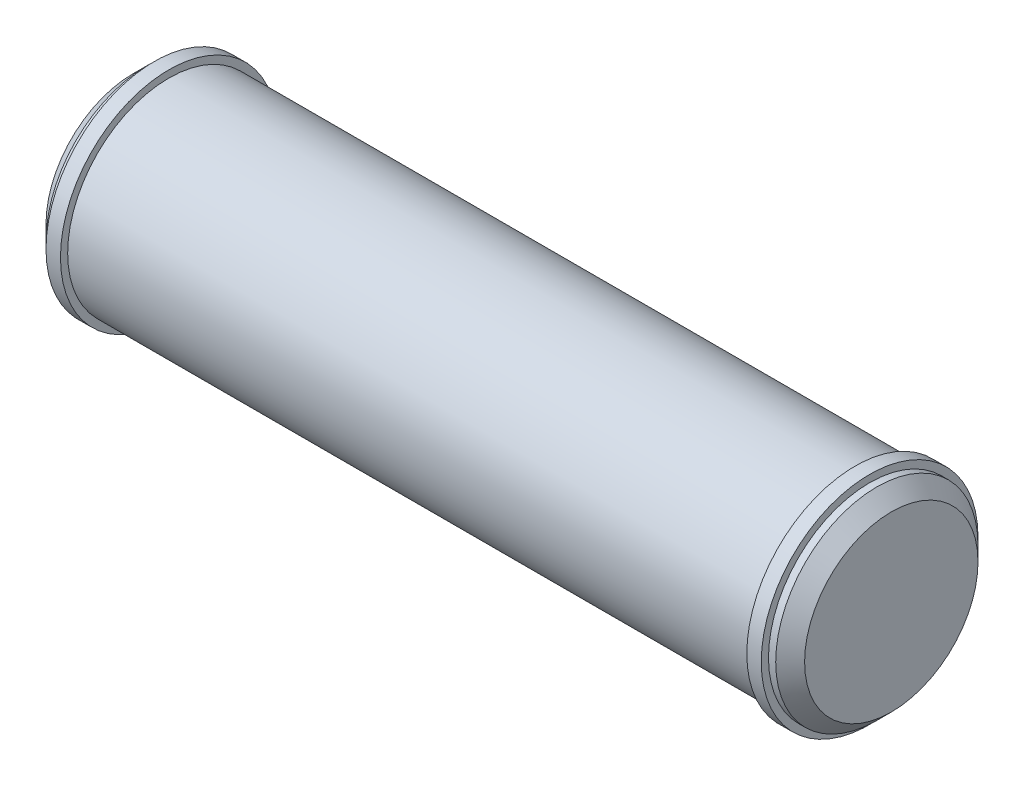
SolidWorks part; units mm, degrees
ref_plane "Front Plane" through (0, 0, 0) normal (0, 0, 1) x (1, 0, 0)
ref_plane "Top Plane" through (0, 0, 0) normal (0, 1, 0) x (1, 0, 0)
ref_plane "Right Plane" through (0, 0, 0) normal (1, 0, 0) x (0, 0, -1)
sketch "Sketch1" plane through (0, 0, 0) normal (0, 0, 1) x (1, 0, 0)
  line L0 (-632.8203, 0) -> (31008.1929, 0) construction
  line L1 (0, -632.8203) -> (0, 31008.1929) construction
  line L2 (-52.5, 0) -> (52.5, 0)
  line L3 (52.5, 0) -> (52.5, 12)
  line L4 (50.5, 14) -> (49.5, 14)
  line L5 (49.5, 14) -> (49.5, 15)
  line L6 (49.5, 15) -> (47.5, 15)
  line L7 (47.5, 15) -> (47.5, 14)
  line L8 (47.5, 14) -> (-47.5, 14)
  line L9 (-47.5, 15) -> (-47.5, 14)
  line L10 (-49.5, 14) -> (-49.5, 15)
  line L11 (-52.5, 0) -> (-52.5, 12)
  line L12 (-50.5, 14) -> (-49.5, 14)
  line L13 (-49.5, 15) -> (-47.5, 15)
  line L14 (52.5, 12) -> (50.5, 14)
  line L15 (-52.5, 12) -> (-50.5, 14)
  point P8 (52.5, 14)
  point P14 (0, 0)
  point P18 (-52.5, 14)
  point P19 (0, 14)
  dimension "D1" = 105
  dimension "D2" = 28
  dimension "D3" = 30
  dimension "D4" = 2
  dimension "D5" = 3
  dimension "D6" = 2
  dimension "D7" = 45
  dimension "D8" = 2
  dimension "D9" = 45
revolve "Revolve3" add sketch "Sketch1" angle 360 about L0
